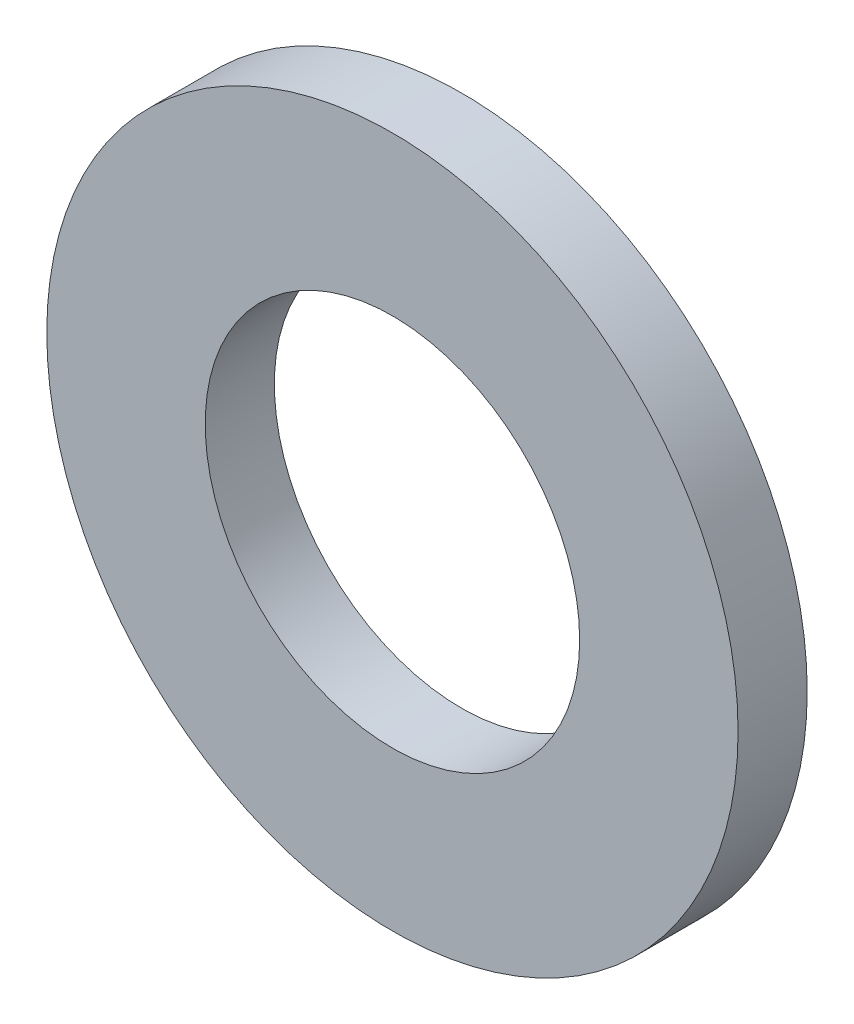
SolidWorks part; units mm, degrees
ref_plane "Plan de face" through (0, 0, 0) normal (0, 0, 1) x (1, 0, 0)
ref_plane "Plan de dessus" through (0, 0, 0) normal (0, 1, 0) x (1, 0, 0)
ref_plane "Plan de droite" through (0, 0, 0) normal (1, 0, 0) x (0, 0, -1)
sketch "Esquisse1" plane through (0, 0, 0) normal (0, 0, 1) x (1, 0, 0)
  circle A0 centre (0, 0) radius 3.25
  circle A1 centre (0, 0) radius 6
  dimension "D1" = 6.5
  dimension "D2" = 12
extrude "Extrusion1" add sketch "Esquisse1" along normal blind 1.2
sketch "Esquisse2" plane through (0, 0, 1.2) normal (0, 0, 1) x (1, 0, 0)
  circle A0 centre (0, 0) radius 6 construction
  point P0 (0, -6)
